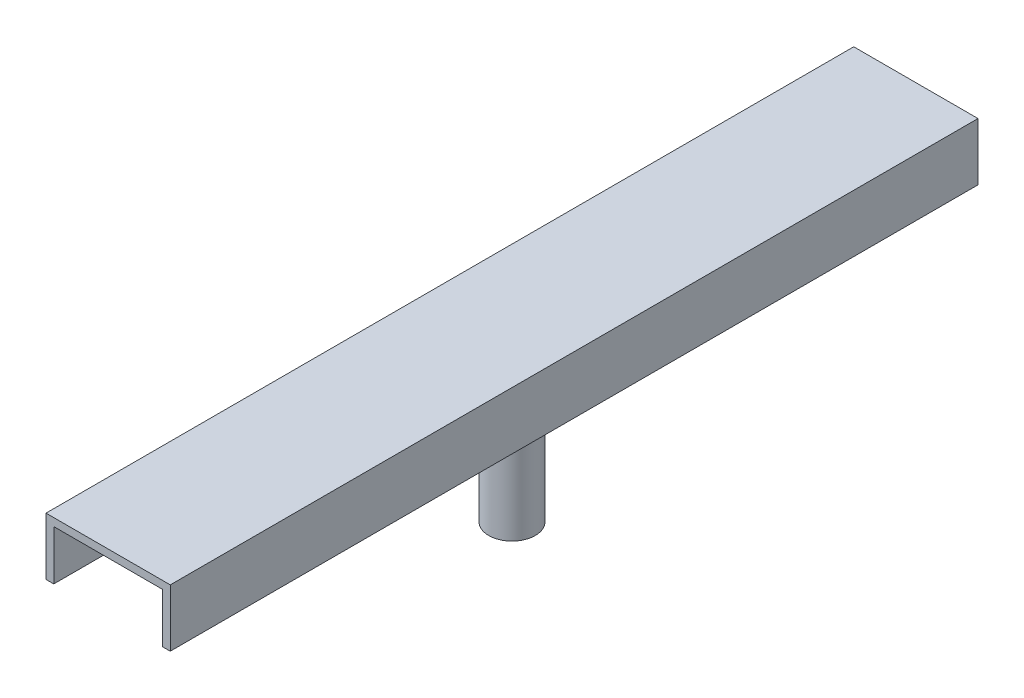
SolidWorks part; units mm, degrees
ref_plane "Front Plane" through (0, 0, 0) normal (0, 0, 1) x (1, 0, 0)
ref_plane "Top Plane" through (0, 0, 0) normal (0, 1, 0) x (1, 0, 0)
ref_plane "Right Plane" through (0, 0, 0) normal (1, 0, 0) x (0, 0, -1)
sketch "Sketch1" plane through (0, 0, 0) normal (0, 0, 1) x (1, 0, 0)
  line L0 (-50.8, -23.495) -> (-44.45, -23.495)
  line L1 (-44.45, -23.495) -> (-44.45, 17.145)
  line L2 (-50.8, -23.495) -> (-50.8, 23.495)
  line L3 (-50.8, 23.495) -> (50.8, 23.495)
  line L4 (50.8, -23.495) -> (50.8, 23.495)
  line L5 (-50.8, -23.495) -> (50.8, 23.495) construction
  line L6 (-50.8, 23.495) -> (50.8, -23.495) construction
  line L7 (-44.45, 17.145) -> (44.45, 17.145)
  line L8 (44.45, 17.145) -> (44.45, -23.495)
  line L9 (44.45, -23.495) -> (50.8, -23.495)
  point P0 (0, 0)
  dimension "D1" = 101.6
  dimension "D2" = 46.99
  dimension "D3" = 6.35
  dimension "D4" = 6.35
extrude "Boss-Extrude1" add sketch "Sketch1" along normal mid plane 660.4
sketch "Sketch2" plane through (0, 17.145, 0) normal (0, -1, 0) x (1, 0, 0)
  circle A0 centre (0, 0) radius 19.05
  dimension "D1" = 38.1
extrude "Boss-Extrude2" add sketch "Sketch2" along normal blind 139.7
equation "\"D4@Sketch1\" = \"D3@Sketch1\""
